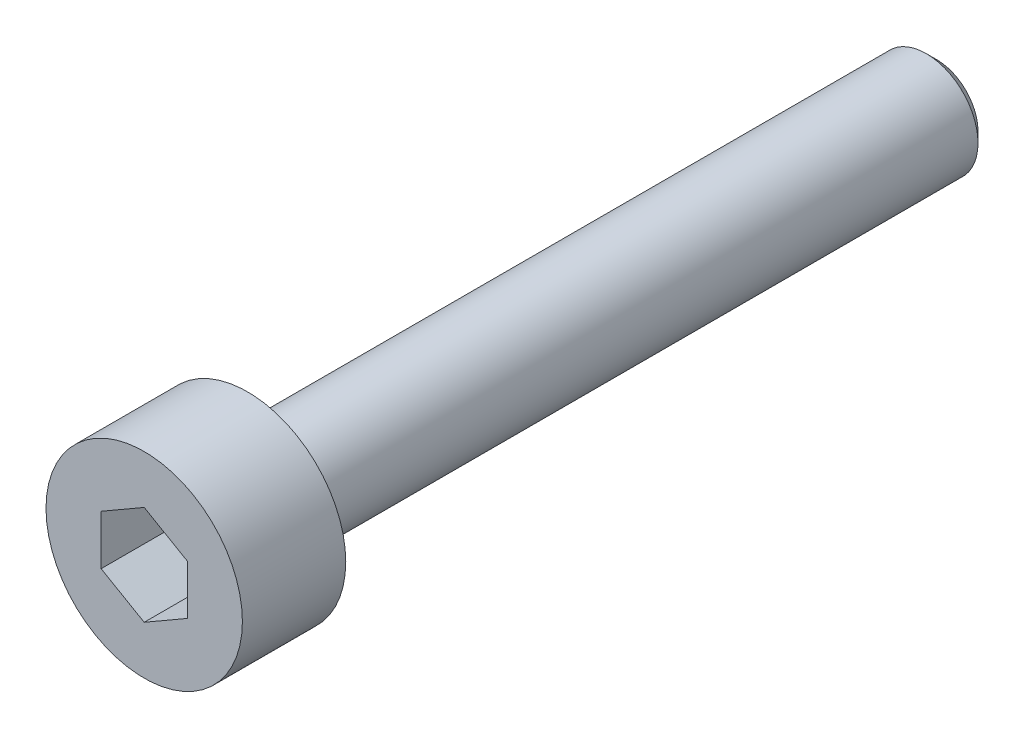
SolidWorks part; units mm, degrees
ref_plane "Front Plane" through (0, 0, 0) normal (0, 0, 1) x (1, 0, 0)
ref_plane "Top Plane" through (0, 0, 0) normal (0, 1, 0) x (1, 0, 0)
ref_plane "Right Plane" through (0, 0, 0) normal (1, 0, 0) x (0, 0, -1)
sketch "Sketch1" plane through (0, 0, 0) normal (0, 0, 1) x (1, 0, 0)
  circle A0 centre (0, 0) radius 2.85
  dimension "D1" = 5.7
extrude "Boss-Extrude1" add sketch "Sketch1" along normal blind 3
sketch "Sketch2" plane through (0, 0, 0) normal (0, 0, -1) x (-1, 0, 0)
  circle A0 centre (0, 0) radius 1.5
  dimension "D1" = 3
extrude "Boss-Extrude2" add sketch "Sketch2" along normal blind 20
chamfer "Chamfer1" distance 0.3 angle 45 1 edges at (-1.5, 0, -20)
sketch "Sketch3" plane through (0, 0, 3) normal (0, 0, 1) x (1, 0, 0)
  line L1 (0, 1.4434) -> (-1.25, 0.7217)
  line L2 (-1.25, 0.7217) -> (-1.25, -0.7217)
  line L3 (-1.25, -0.7217) -> (0, -1.4434)
  line L4 (0, -1.4434) -> (1.25, -0.7217)
  line L5 (1.25, -0.7217) -> (1.25, 0.7217)
  line L6 (1.25, 0.7217) -> (0, 1.4434)
  circle A0 centre (0, 0) radius 1.25 construction
  dimension "D1" = 2.5
extrude "Cut-Extrude1" cut sketch "Sketch3" against normal blind 2
